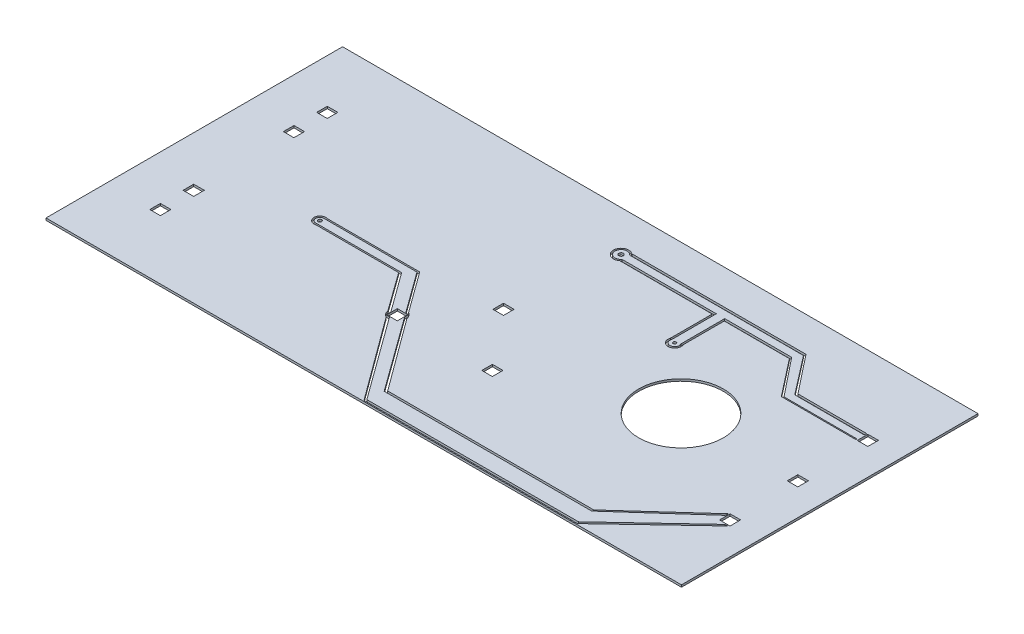
SolidWorks part; units mm, degrees
ref_plane "Front" through (0, 0, 0) normal (0, 0, 1) x (1, 0, 0)
ref_plane "Top" through (0, 0, 0) normal (0, 1, 0) x (1, 0, 0)
ref_plane "Right" through (0, 0, 0) normal (1, 0, 0) x (0, 0, -1)
sketch "Sketch1" plane through (0, 0, 0) normal (0, 1, 0) x (1, 0, 0)
  line L0 (-30, 0) -> (0, 0)
  line L2 (0, 0) -> (0, 14)
  line L3 (0, 14) -> (-30, 14)
  line L4 (-30, 0) -> (-30, 14)
  line L5 (0, 0) -> (-30, 14) construction
  line L6 (0, 14) -> (-30, 0) construction
  line L7 (-1.2567, 10.055) -> (-1.7559, 10.055)
  line L8 (-1.2565, 6.7493) -> (-1.7557, 6.7493)
  line L9 (-1.2565, 6.7493) -> (-1.2565, 7.2507)
  line L10 (-1.2565, 7.2507) -> (-1.7557, 7.2507)
  line L11 (-1.7557, 6.7493) -> (-1.7557, 7.2507)
  line L12 (-1.2565, 6.7493) -> (-1.7557, 7.2507) construction
  line L13 (-1.2565, 7.2507) -> (-1.7557, 6.7493) construction
  line L14 (-1.2567, 10.055) -> (-1.2567, 10.5565)
  line L15 (-1.2567, 10.5565) -> (-1.7559, 10.5565)
  line L16 (-1.7559, 10.055) -> (-1.7559, 10.5565)
  line L17 (-4.961, 0.047) -> (-1.3117, 3.4982)
  line L18 (-1.2565, 3.5505) -> (-1.7557, 3.5505)
  line L19 (-1.2565, 3.5505) -> (-1.2565, 4.0519)
  line L20 (-1.2565, 4.0519) -> (-1.7557, 4.0519)
  line L21 (-1.7557, 3.5505) -> (-1.7557, 4.0519)
  line L22 (-7.1446, 12.3643) -> (-6.4862, 12.3643)
  line L23 (-1.8034, 4.0087) -> (-5.1351, 0.9919)
  line L24 (-7.1446, 12.3643) -> (-14.7062, 12.3643)
  line L25 (-14.861, 0.9919) -> (-5.1351, 0.9919)
  line L26 (-17.9266, 3.9856) -> (-15.0345, 0.047)
  line L28 (-17.3631, 4.3994) -> (-14.861, 0.9919)
  line L29 (-17.5003, 4.0848) -> (-17.9995, 4.0848)
  line L30 (-17.5003, 4.0848) -> (-17.5003, 4.5862)
  line L31 (-17.5003, 4.5862) -> (-17.9995, 4.5862)
  line L32 (-17.9995, 4.0848) -> (-17.9995, 4.5862)
  line L33 (-17.9995, 4.5862) -> (-17.5003, 4.0848) construction
  line L34 (-17.5003, 4.5862) -> (-17.9995, 4.0848) construction
  line L35 (-14.7062, 11.7963) -> (-10.3452, 11.7963)
  line L36 (-1.4798, 3.4636) -> (-5.0107, 0.1474)
  line L38 (-18.1378, 4.2791) -> (-19.4413, 6.0904)
  line L39 (-19.4413, 6.0904) -> (-23.34, 6.0904)
  line L40 (-15, 0.1474) -> (-5.0107, 0.1474)
  line L41 (-23.34, 6.613) -> (-18.9702, 6.613)
  line L43 (-19.3704, 6.1609) -> (-18.0143, 4.295)
  line L44 (-23.4236, 6.1609) -> (-19.3704, 6.1609)
  line L45 (-23.4236, 6.5425) -> (-19.0292, 6.5425)
  line L46 (-19.0292, 6.5425) -> (-17.6284, 4.6128)
  line L47 (-14.9305, 0.8962) -> (-17.4878, 4.4191)
  line L48 (-14.9305, 0.8962) -> (-5.1351, 0.8962)
  line L49 (-5.1351, 0.8962) -> (-1.845, 3.838)
  line L50 (-1.8142, 10.5565) -> (-5.0569, 10.5565)
  line L51 (-17.8488, 4.0673) -> (-15, 0.1474)
  line L52 (-17.5664, 4.682) -> (-18.9702, 6.613)
  line L53 (-14.7062, 11.9045) -> (-10.2587, 11.9045)
  line L54 (-12.9795, 4.0516) -> (-13.4787, 4.0516)
  line L55 (-12.9795, 4.0516) -> (-12.9795, 4.5531)
  line L56 (-12.9795, 4.5531) -> (-13.4787, 4.5531)
  line L57 (-13.4787, 4.0516) -> (-13.4787, 4.5531)
  line L58 (-9.775, 11.7963) -> (-6.7005, 11.7963)
  line L59 (-15.2154, 6.812) -> (-15.7146, 6.812)
  line L60 (-15.2154, 6.812) -> (-15.2154, 7.3135)
  line L61 (-15.2154, 7.3135) -> (-15.7146, 7.3135)
  line L62 (-15.7146, 6.812) -> (-15.7146, 7.3135)
  line L63 (-15.2154, 7.3135) -> (-15.7146, 6.812) construction
  line L64 (-15.7146, 7.3135) -> (-15.2154, 6.812) construction
  line L65 (-14.7062, 12.2561) -> (-6.4949, 12.2561)
  line L71 (-5.3393, 10.055) -> (-6.7005, 11.7963)
  line L73 (-6.4862, 12.3643) -> (-5.0569, 10.5565)
  line L74 (-6.7005, 11.9045) -> (-5.2666, 10.1079)
  line L75 (-5.0934, 10.4439) -> (-6.4949, 12.2561)
  line L76 (-5.3393, 10.055) -> (-1.8142, 10.055)
  line L77 (-1.8142, 10.1079) -> (-5.2666, 10.1079)
  line L79 (-9.775, 11.7963) -> (-9.775, 9.8601)
  line L81 (-10.2587, 9.813) -> (-10.2587, 11.9045)
  line L83 (-9.8634, 11.9045) -> (-9.8634, 9.8405)
  line L84 (-4.961, 0.047) -> (-15.0345, 0.047)
  line L85 (-9.8634, 11.9045) -> (-6.7005, 11.9045)
  line L86 (-5.0934, 10.4439) -> (-1.8142, 10.4439)
  line L87 (-10.3452, 11.7963) -> (-10.3452, 9.8322)
  line L89 (-1.8142, 10.5565) -> (-1.8142, 10.4439)
  line L93 (-27.3947, 2.7937) -> (-27.8939, 2.7937)
  line L94 (-27.3947, 2.7937) -> (-27.3947, 3.2952)
  line L95 (-27.3947, 3.2952) -> (-27.8939, 3.2952)
  line L96 (-27.8939, 2.7937) -> (-27.8939, 3.2952)
  line L98 (-27.3947, 4.3663) -> (-27.8939, 4.3663)
  line L99 (-27.3947, 4.3663) -> (-27.3947, 4.8678)
  line L100 (-27.3947, 4.8678) -> (-27.8939, 4.8678)
  line L101 (-27.8939, 4.3663) -> (-27.8939, 4.8678)
  line L117 (-27.4283, 9.1322) -> (-27.9275, 9.1322)
  line L118 (-27.4283, 9.1322) -> (-27.4283, 9.6337)
  line L119 (-27.4283, 9.6337) -> (-27.9275, 9.6337)
  line L120 (-27.9275, 9.1322) -> (-27.9275, 9.6337)
  line L121 (-27.4283, 10.7048) -> (-27.9275, 10.7048)
  line L122 (-27.4283, 10.7048) -> (-27.4283, 11.2063)
  line L123 (-27.4283, 11.2063) -> (-27.9275, 11.2063)
  line L124 (-27.9275, 10.7048) -> (-27.9275, 11.2063)
  line L126 (-1.8034, 4.0087) -> (-1.8034, 3.8753)
  line L129 (-1.443, 3.4982) -> (-1.3117, 3.4982)
  line L134 (-18.0143, 4.295) -> (-18.0143, 4.0673)
  line L135 (-18.0143, 4.0673) -> (-17.8488, 4.0673)
  line L136 (-17.4878, 4.4191) -> (-17.4878, 4.6008)
  line L137 (-17.4878, 4.6008) -> (-17.6284, 4.6128)
  line L138 (-1.845, 3.838) -> (-1.8034, 3.8753)
  line L139 (-1.443, 3.4982) -> (-1.4798, 3.4636)
  line L140 (-1.8142, 10.1079) -> (-1.8142, 10.055)
  circle A0 centre (-7.0204, 7) radius 2
  arc A1 (-17.3631, 4.3994) -> (-17.5664, 4.682) centre (-17.7499, 4.3355) ccw
  arc A2 (-18.1378, 4.2791) -> (-17.9266, 3.9856) centre (-17.7499, 4.3355) ccw
  arc A3 (-23.34, 6.613) -> (-23.34, 6.0904) centre (-23.4236, 6.3517) ccw
  arc A4 (-23.4236, 6.5425) -> (-23.4236, 6.1609) centre (-23.4236, 6.3517) ccw
  arc A5 (-14.7062, 12.3643) -> (-14.7062, 11.7963) centre (-14.9305, 12.0803) ccw
  arc A6 (-14.7062, 12.2561) -> (-14.7062, 11.9045) centre (-14.9305, 12.0803) ccw
  arc A12 (-10.3452, 9.8322) -> (-9.775, 9.8601) centre (-10.0546, 9.7343) ccw
  arc A13 (-10.2587, 9.813) -> (-9.8634, 9.8405) centre (-10.0546, 9.7343) ccw
  circle A14 centre (-10.0546, 9.7343) radius 0.0697
  circle A15 centre (-14.9305, 12.0803) radius 0.1045
  circle A16 centre (-23.4236, 6.3517) radius 0.0849
  point P4 (-15, 7)
  point P13 (-1.5061, 7)
  dimension "D1" = 30
  dimension "D2" = 14
extrude "Boss-Extrude2" add sketch "Sketch1" along normal blind 0.1
